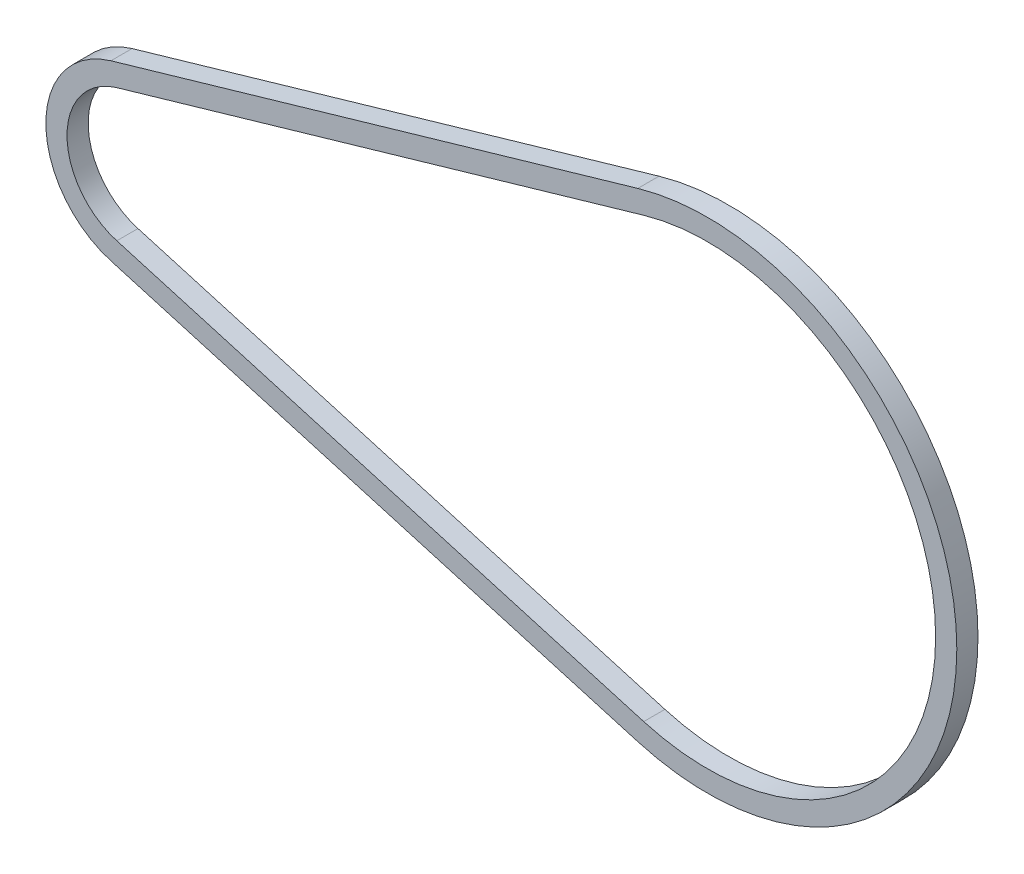
SolidWorks part; units mm, degrees
ref_plane "Front Plane" through (0, 0, 0) normal (0, 0, 1) x (1, 0, 0)
ref_plane "Top Plane" through (0, 0, 0) normal (0, 1, 0) x (1, 0, 0)
ref_plane "Right Plane" through (0, 0, 0) normal (1, 0, 0) x (0, 0, -1)
sketch "Sketch1" plane through (0, 0, 0) normal (0, 0, 1) x (1, 0, 0)
  line L0 (-2.6618, 9.1708) -> (60.5315, 27.5125)
  line L1 (0, 0) -> (68.5169, 0) construction
  line L2 (-2.6618, -9.1708) -> (60.5315, -27.5125)
  arc A0 (-2.6618, 9.1708) -> (-2.6618, -9.1708) centre (0, 0) ccw
  arc A1 (60.5315, -27.5125) -> (60.5315, 27.5125) centre (68.5169, 0) ccw
  point P1 (60.5315, 27.5125)
  point P9 (61.8443, 27.5513)
  dimension "D1" = 19.0986
  dimension "D2" = 57.2958
extrude "Extrude-Thin1" add sketch "Sketch1" along normal mid plane 2.54 thin thin type mid plane wall 2.54
equation "\"n1\"= 20"
equation "\"n2\"= 60"
equation "\"p\"= 3mm"
equation "\"D1@Sketch1\"=\"n1\"*\"p\"/pi"
equation "\"D2@Sketch1\"=\"n2\"*\"p\"/pi"
